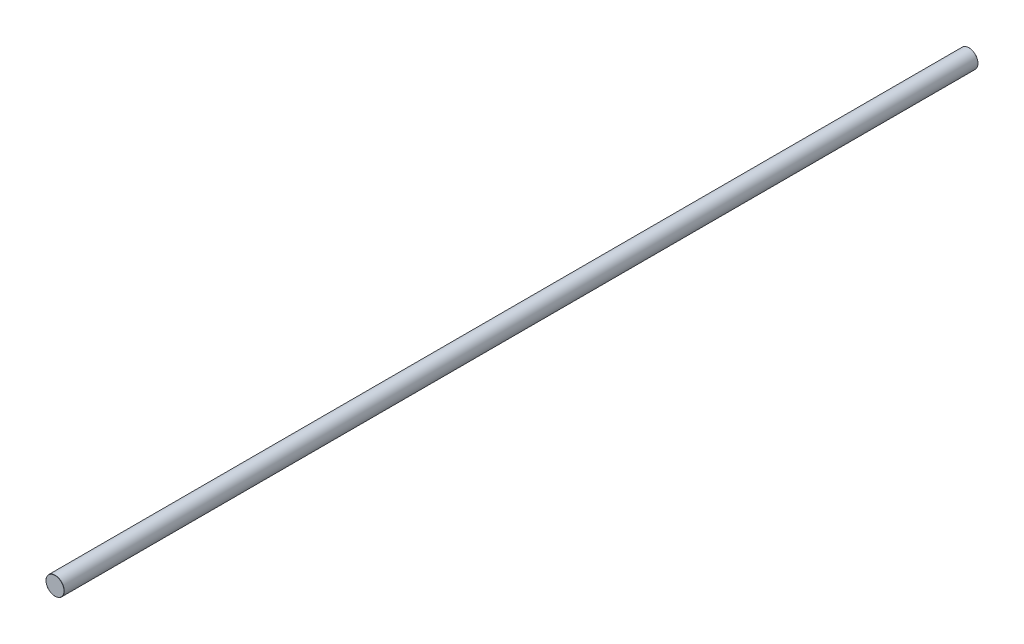
SolidWorks part; units mm, degrees
ref_plane "Front Plane" through (0, 0, 0) normal (0, 0, 1) x (1, 0, 0)
ref_plane "Top Plane" through (0, 0, 0) normal (0, 1, 0) x (1, 0, 0)
ref_plane "Right Plane" through (0, 0, 0) normal (1, 0, 0) x (0, 0, -1)
sketch "Sketch1" plane through (0, 0, 0) normal (0, 0, 1) x (1, 0, 0)
  circle A0 centre (0, 0) radius 5
extrude "Boss-Extrude1" add sketch "Sketch1" along normal blind 500
fillet "Fillet1" radius 0.1 2 edges at (5, 0, 0) (5, 0, 500)
